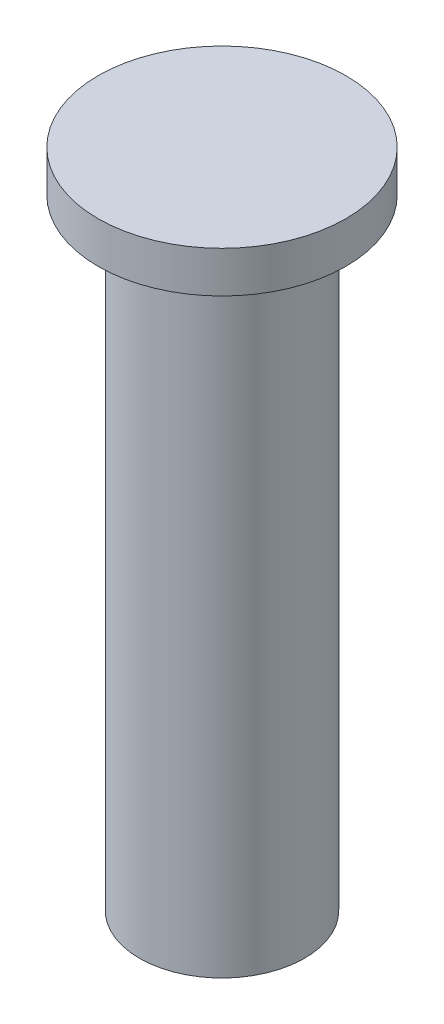
SolidWorks part; units mm, degrees
ref_plane "Front Plane" through (0, 0, 0) normal (0, 0, 1) x (1, 0, 0)
ref_plane "Top Plane" through (0, 0, 0) normal (0, 1, 0) x (1, 0, 0)
ref_plane "Right Plane" through (0, 0, 0) normal (1, 0, 0) x (0, 0, -1)
sketch "Sketch1" plane through (0, 0, 0) normal (0, 1, 0) x (1, 0, 0)
  circle A0 centre (0, 0) radius 5.075
  dimension "D1" = 10.15
extrude "Boss-Extrude1" add sketch "Sketch1" along normal blind 38.1
sketch "Sketch2" plane through (0, 38.1, 0) normal (0, 1, 0) x (1, 0, 0)
  circle A0 centre (0, 0) radius 7.615
  circle A1 centre (0, 0) radius 5.075 construction
  dimension "D1" = 2.54
extrude "Boss-Extrude2" add sketch "Sketch2" along normal blind 2.54
